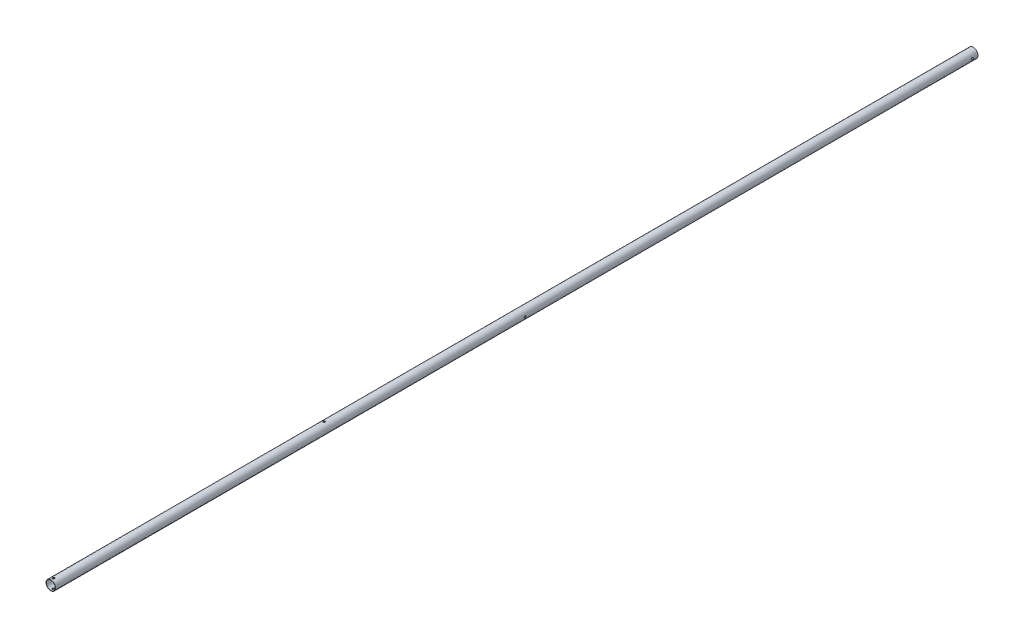
SolidWorks part; units mm, degrees
material "1060 Alloy"
ref_plane "Front Plane" through (0, 0, 0) normal (0, 0, 1) x (1, 0, 0)
ref_plane "Top Plane" through (0, 0, 0) normal (0, 1, 0) x (1, 0, 0)
ref_plane "Right Plane" through (0, 0, 0) normal (1, 0, 0) x (0, 0, -1)
sketch "Sketch1" plane through (0, 0, 0) normal (0, 0, 1) x (1, 0, 0)
  circle A0 centre (0, 0) radius 12.7
  circle A1 centre (0, 0) radius 11.9063
  dimension "D1" = 25.4
  dimension "D2" = 23.8125
extrude "Boss-Extrude1" add sketch "Sketch1" along normal blind 2443.8722
sketch "Sketch2" plane through (0, 0, 0) normal (0, 1, 0) x (1, 0, 0)
  line L0 (0, -2443.8722) -> (0, -2436.6222) construction
  line L1 (-12.7, -2443.8722) -> (12.7, -2443.8722) construction
  dimension "D1" = 7.25
hole_wizard "M5 Clearance Hole1" positions "Sketch3" profile "Sketch4" hole size "M5" standard "AS"
sketch "Sketch3" plane through (0, 0, 0) normal (0, 1, 0) x (1, 0, 0)
  point P0 (0, -2436.6222)
sketch "Sketch4" plane through (0, 0, 2436.6222) normal (1, 0, 0) x (0, 0, -1)
  line L0 (0, 0) -> (0, 12.7)
  line L1 (0, 12.7) -> (2.75, 12.7)
  line L2 (2.75, 12.7) -> (2.75, 0)
  line L5 (2.75, 0) -> (0, 0)
  line L11 (0, -6.35) -> (0, 107.95) construction
  dimension "Thru Hole Dia." = 5.5
  dimension "Thru Hole Depth" = 12.7
mirror "Mirror1" about plane through (0, 0, 0) normal (0, 1, 0) of "M5 Clearance Hole1"
sketch "Sketch5" plane through (0, 0, 0) normal (1, 0, 0) x (0, 0, -1)
  line L0 (0, 0) -> (-15, 0) construction
  dimension "D1" = 15
hole_wizard "M5 Clearance Hole3" positions "Sketch11" profile "Sketch12" hole size "M5" standard "AS"
sketch "Sketch11" plane through (0, 0, 0) normal (1, 0, 0) x (0, 0, -1)
  point P0 (-15, 0)
sketch "Sketch12" plane through (0, 0, 15) normal (0, 1, 0) x (0, 0, 1)
  line L0 (0, 0) -> (0, 12.7)
  line L1 (0, 12.7) -> (2.75, 12.7)
  line L2 (2.75, 12.7) -> (2.75, 0)
  line L5 (2.75, 0) -> (0, 0)
  line L11 (0, -6.35) -> (0, 107.95) construction
  dimension "Thru Hole Dia." = 5.5
  dimension "Thru Hole Depth" = 12.7
mirror "Mirror3" about plane through (0, 0, 0) normal (1, 0, 0) of "M5 Clearance Hole3"
sketch "Sketch13" plane through (0, 0, 0) normal (0, 1, 0) x (1, 0, 0)
  circle A0 centre (-0.7398, -1718.7545) radius 2.75
extrude "Cut-Extrude1" cut sketch "Sketch13" against normal through all both and the other way through all
sketch "Sketch14" plane through (0, 0, 0) normal (1, 0, 0) x (0, 0, -1)
  circle A0 centre (-1200, 0) radius 2.5
  dimension "D1" = 5
  dimension "D2" = 1200
extrude "Cut-Extrude2" cut sketch "Sketch14" against normal through all both and the other way through all
equation "\"keelOutDiameter\"= 1in"
equation "\"keelInDiameter\"= \"keelOutDiameter\" - 0.125in"
equation "\"frontBoltClearance\"= 7.25mm"
equation "\"betweenBoltsDistance\"= 20mm"
equation "\"D1@Sketch2\"=\"frontBoltClearance\""
equation "\"wingLength\"= 1.4m"
equation "\"frontTubeLength\"= \"wingLength\" / sin ( 34.95deg )"
equation "\"D1@Boss-Extrude1\"=\"frontTubeLength\""
equation "\"D1@Sketch1\"=\"keelOutDiameter\""
equation "\"D2@Sketch1\"=\"keelOutDiameter\"-0.0625in"
